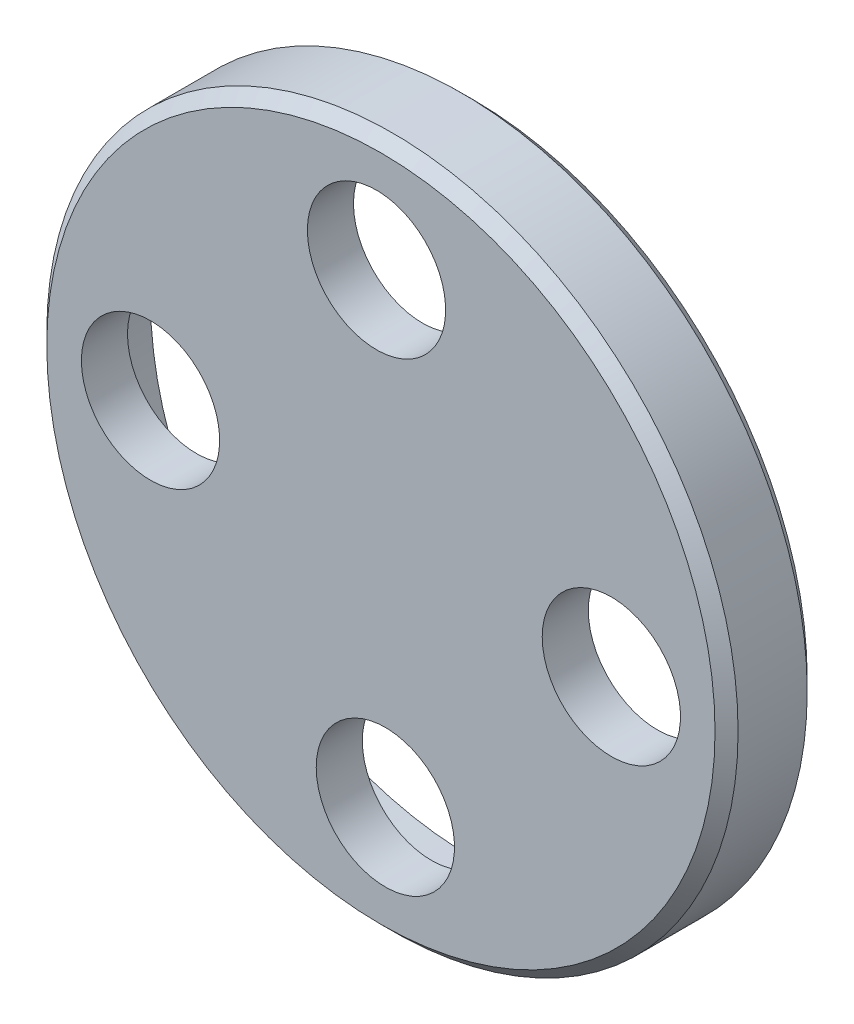
SolidWorks part; units mm, degrees
ref_plane "Спереди" through (0, 0, 0) normal (0, 0, 1) x (1, 0, 0)
ref_plane "Сверху" through (0, 0, 0) normal (0, 1, 0) x (1, 0, 0)
ref_plane "Справа" through (0, 0, 0) normal (1, 0, 0) x (0, 0, -1)
sketch "Эскиз1" plane through (0, 0, 0) normal (0, 0, 1) x (1, 0, 0)
  circle A0 centre (0, 0) radius 15
extrude "Вытянуть1" add sketch "Эскиз1" along normal blind 4
sketch "Эскиз3" plane through (0, 0, 0) normal (0, 0, -1) x (-1, 0, 0)
  circle A0 centre (0, 0) radius 14
extrude "Вытянуть2" cut sketch "Эскиз3" against normal blind 2
sketch "Эскиз5" plane through (0, 0, 2) normal (0, 0, -1) x (-1, 0, 0)
  line L0 (9.9981, 0.1927) -> (-0.1927, -9.9981) construction
  line L1 (9.9981, 0.1927) -> (0.1909, 10) construction
  circle A0 centre (9.9981, 0.1927) radius 3
  circle A1 centre (-0.1927, -9.9981) radius 3
  circle A2 centre (0.1909, 10) radius 3
  circle A3 centre (-10, -0.1909) radius 3
  dimension "D1" = 10
  dimension "D2" = 90
  dimension "D3" = 10
  dimension "D4" = 10
  dimension "D5" = 10
extrude "Вытянуть3" cut sketch "Эскиз5" against normal through all
chamfer "Фаска1" distance 0.5 angle 45 1 edges at (15, 0, 4)
chamfer "Фаска3" distance 0.5 angle 45 1 edges at (15, 0, 0)
